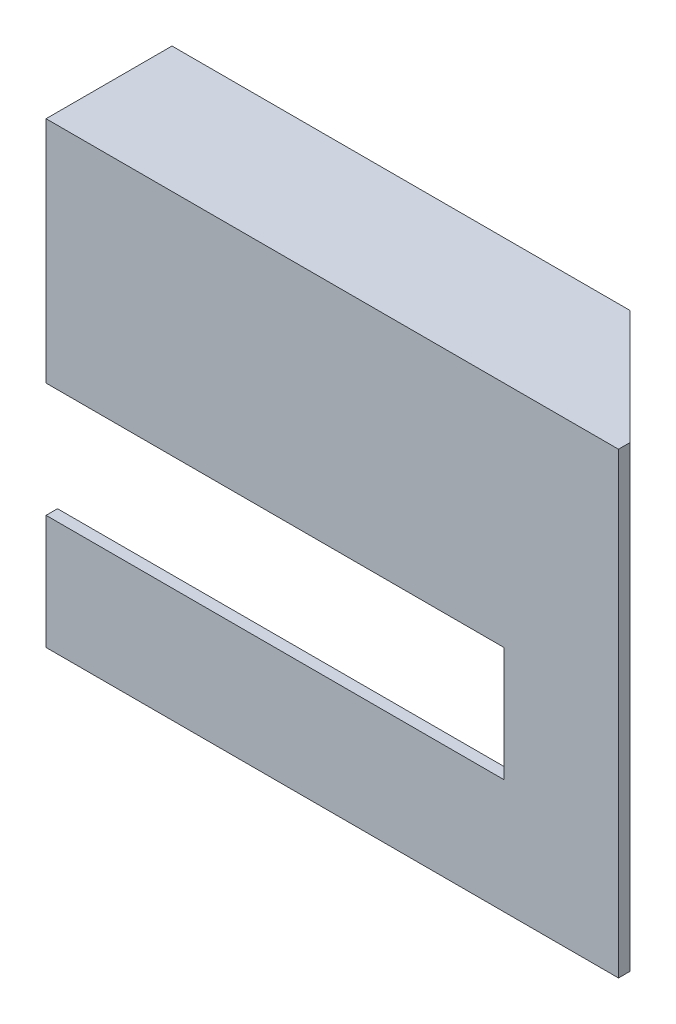
SolidWorks part; units mm, degrees
ref_plane "前视基准面" through (0, 0, 0) normal (0, 0, 1) x (1, 0, 0)
ref_plane "上视基准面" through (0, 0, 0) normal (0, 1, 0) x (1, 0, 0)
ref_plane "右视基准面" through (0, 0, 0) normal (1, 0, 0) x (0, 0, -1)
sketch "草图1" plane through (0, 0, 0) normal (0, 0, 1) x (1, 0, 0)
  line L0 (19.887, -8.0452) -> (19.887, -18.0452)
  line L1 (-20.113, 11.9548) -> (29.887, 11.9548)
  line L2 (-20.113, 11.9548) -> (-20.113, -8.0452)
  line L3 (-20.113, -8.0452) -> (19.887, -8.0452)
  line L4 (29.887, 11.9548) -> (29.887, -17.7643)
  line L5 (-20.113, 11.9548) -> (29.887, -17.7643) construction
  line L6 (-20.113, -8.0452) -> (29.887, 11.9548) construction
  line L7 (19.887, -18.0452) -> (-20.113, -18.0452)
  line L8 (-20.113, -18.0452) -> (-20.113, -28.0452)
  line L9 (-20.113, -28.0452) -> (29.887, -28.0452)
  line L10 (29.887, -17.7643) -> (29.887, -28.0452)
  point P0 (0, 0)
  dimension "D1" = 10
  dimension "D2" = 10
  dimension "D3" = 40
  dimension "D4" = 10
  dimension "D5" = 50
extrude "凸台-拉伸2" add sketch "草图1" along normal blind 1
sketch "草图3" plane through (0, 0, 0) normal (0, 0, -1) x (-1, 0, 0)
  line L0 (-29.887, 11.9548) -> (20.113, 11.9548)
  line L1 (20.113, 11.9548) -> (20.113, 10.9548)
  line L2 (20.113, 11.9548) -> (20.113, -8.0452) construction
  line L3 (20.113, 10.9548) -> (-29.887, 10.9548)
  line L4 (-29.887, -28.0452) -> (-29.887, 11.9548) construction
  line L5 (-29.887, 10.9548) -> (-29.887, 11.9548)
extrude "凸台-拉伸4" add sketch "草图3" along normal blind 10
chamfer "倒角1" distance 10 angle 45 1 edges at (29.887, 11.4548, -10)
